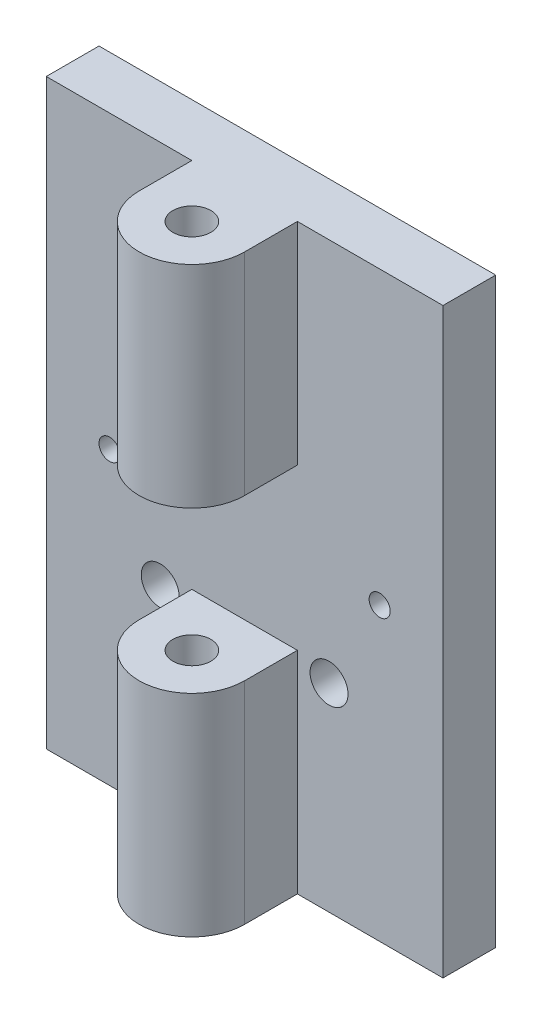
SolidWorks part; units mm, degrees
ref_plane "Front Plane" through (0, 0, 0) normal (0, 0, 1) x (1, 0, 0)
ref_plane "Top Plane" through (0, 0, 0) normal (0, 1, 0) x (1, 0, 0)
ref_plane "Right Plane" through (0, 0, 0) normal (1, 0, 0) x (0, 0, -1)
sketch "Sketch2" plane through (0, 0, 0) normal (0, 0, 1) x (1, 0, 0)
  line L1 (-11.938, 0) -> (11.938, 0)
  line L2 (-11.938, 0) -> (-11.938, 35.052)
  line L3 (-11.938, 35.052) -> (11.938, 35.052)
  line L4 (11.938, 0) -> (11.938, 35.052)
  circle A1 centre (-5.08, 11.938) radius 1.143
  circle A3 centre (5.08, 11.938) radius 1.143
  circle A5 centre (-8.128, 17.526) radius 0.635
  circle A6 centre (8.128, 17.526) radius 0.635
  dimension "D3" = 17.526
  dimension "D4" = 2.286
  dimension "D5" = 2.286
  dimension "D6" = 17.526
  dimension "D7" = 1.27
  dimension "D8" = 1.27
  dimension "D1" = 23.876
  dimension "D2" = 35.052
  dimension "D9" = 3.81
  dimension "D10" = 3.81
  dimension "D11" = 11.938
  dimension "D12" = 11.938
  dimension "D13" = 10.16
  dimension "D14" = 6.858
extrude "Boss-Extrude1" add sketch "Sketch2" along normal blind 3.175
sketch "Sketch3" plane through (0, 0, 3.175) normal (0, 0, 1) x (1, 0, 0)
  line L0 (-11.938, 0) -> (11.938, 0) construction
  line L1 (-3.175, 0) -> (3.175, 0)
  line L2 (-3.175, 0) -> (-3.175, 35.052)
  line L3 (-3.175, 35.052) -> (3.175, 35.052)
  line L4 (3.175, 0) -> (3.175, 35.052)
  line L5 (11.938, 35.052) -> (-11.938, 35.052) construction
  dimension "D1" = 6.35
extrude "Boss-Extrude2" add sketch "Sketch3" along normal blind 6.35
sketch "Sketch4" plane through (0, 0, 0) normal (0, 1, 0) x (1, 0, 0)
  line L0 (-3.175, -9.525) -> (-3.175, -3.175) construction
  line L2 (3.175, -9.525) -> (-3.175, -9.525) construction
  circle A0 centre (0, -6.35) radius 1.143
  point P6 (-0.1224, -9.525)
  dimension "D3" = 2.286
  dimension "D1" = 3.175
  dimension "D2" = 3.175
extrude "Cut-Extrude3" cut sketch "Sketch4" along normal blind 49.53 contours A0
sketch "Sketch5" plane through (0, 0, 0) normal (1, 0, 0) x (0, 0, -1)
  line L0 (-9.525, 0) -> (-9.525, 35.052) construction
  line L1 (-9.525, 12.7) -> (-3.175, 12.7)
  line L2 (-9.525, 12.7) -> (-9.525, 22.352)
  line L3 (-9.525, 22.352) -> (-3.175, 22.352)
  line L4 (-3.175, 12.7) -> (-3.175, 22.352)
  line L5 (-3.175, 0) -> (-3.175, 35.052) construction
  line L6 (-9.525, 0) -> (-3.175, 0) construction
  line L7 (-9.525, 35.052) -> (-3.175, 35.052) construction
  dimension "D1" = 12.7
  dimension "D2" = 12.7
extrude "Cut-Extrude4" cut sketch "Sketch5" against normal mid plane 49.53
sketch "Sketch6" plane through (0, 0, 0) normal (0, 1, 0) x (1, 0, 0)
  line L0 (-3.175, -9.525) -> (-3.175, -3.175) construction
  line L1 (3.175, -9.525) -> (3.175, -3.175) construction
  line L2 (-3.175, -6.35) -> (-3.175, -9.525)
  line L3 (-3.175, -9.525) -> (0, -9.525)
  line L4 (0, -9.525) -> (3.175, -9.525)
  line L5 (3.175, -9.525) -> (3.175, -6.35)
  arc A0 (-3.175, -6.35) -> (3.175, -6.35) centre (0, -6.35) ccw
extrude "Cut-Extrude5" cut sketch "Sketch6" along normal blind 49.53 contours A0 L2 L3 | A0 L4 L5
